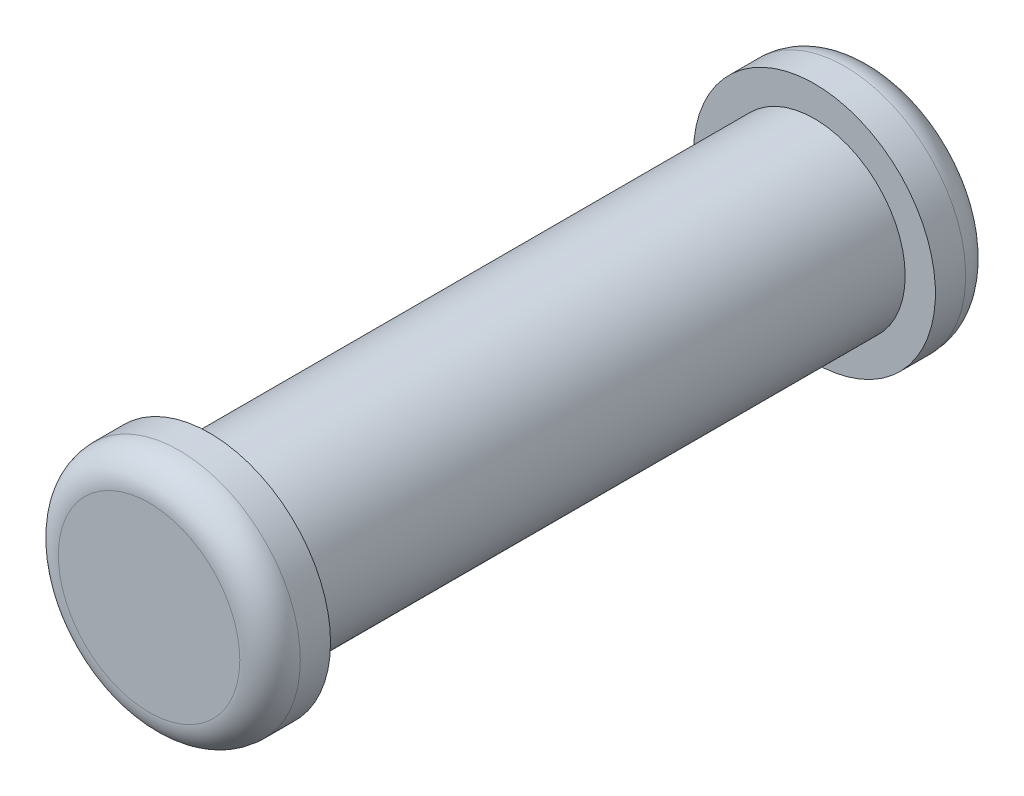
SolidWorks part; units mm, degrees
ref_plane "Front Plane" through (0, 0, 0) normal (0, 0, 1) x (1, 0, 0)
ref_plane "Top Plane" through (0, 0, 0) normal (0, 1, 0) x (1, 0, 0)
ref_plane "Right Plane" through (0, 0, 0) normal (1, 0, 0) x (0, 0, -1)
sketch "Sketch1" plane through (0, 0, 0) normal (0, 0, 1) x (1, 0, 0)
  circle A0 centre (0, 0) radius 1.5
  dimension "D1" = 3
extrude "Boss-Extrude1" add sketch "Sketch1" along normal blind 10
sketch "Sketch2" plane through (0, 0, 0) normal (0, 0, -1) x (-1, 0, 0)
  circle A0 centre (0, 0) radius 2
  dimension "D1" = 4
extrude "Boss-Extrude2" add sketch "Sketch2" along normal blind 1
sketch "Sketch3" plane through (0, 0, 10) normal (0, 0, 1) x (1, 0, 0)
  circle A1 centre (0, 0) radius 2
  circle A2 centre (0, 0) radius 2
  dimension "D1" = 0
extrude "Boss-Extrude3" add sketch "Sketch3" along normal blind 1
fillet "Fillet1" radius 0.5 2 edges at (-2, 0, -1) (2, 0, 11)
